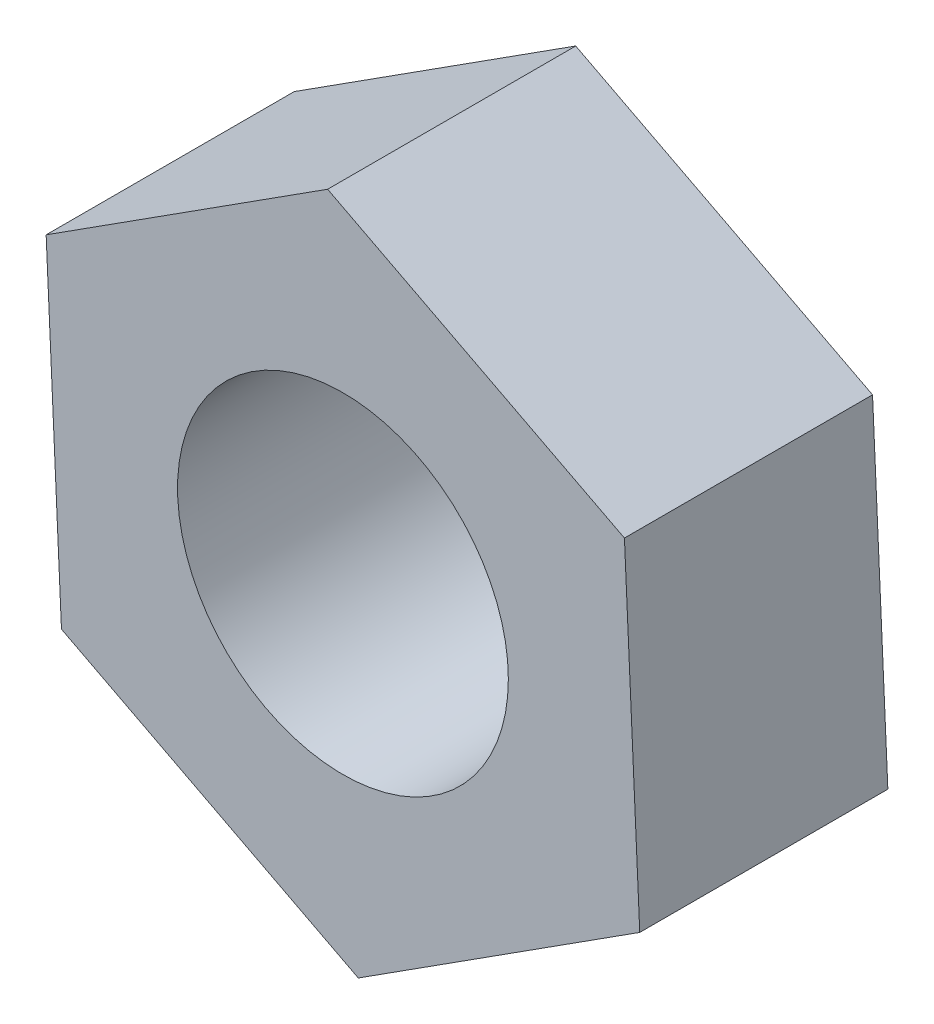
SolidWorks part; units mm, degrees
ref_plane "前视基准面" through (0, 0, 0) normal (0, 0, 1) x (1, 0, 0)
ref_plane "上视基准面" through (0, 0, 0) normal (0, 1, 0) x (1, 0, 0)
ref_plane "右视基准面" through (0, 0, 0) normal (1, 0, 0) x (0, 0, -1)
sketch "草图1" plane through (0, 0, 0) normal (0, 0, 1) x (1, 0, 0)
  line L1 (3.589, -1.8581) -> (3.4037, 2.1791)
  line L2 (3.4037, 2.1791) -> (-0.1853, 4.0372)
  line L3 (-0.1853, 4.0372) -> (-3.589, 1.8581)
  line L4 (-3.589, 1.8581) -> (-3.4037, -2.1791)
  line L5 (-3.4037, -2.1791) -> (0.1853, -4.0372)
  line L6 (0.1853, -4.0372) -> (3.589, -1.8581)
  circle A0 centre (0, 0) radius 3.5 construction
  circle A1 centre (0, 0) radius 2
  dimension "D2" = 4
  dimension "D1" = 7
extrude "凸台-拉伸1" add sketch "草图1" along normal blind 3
